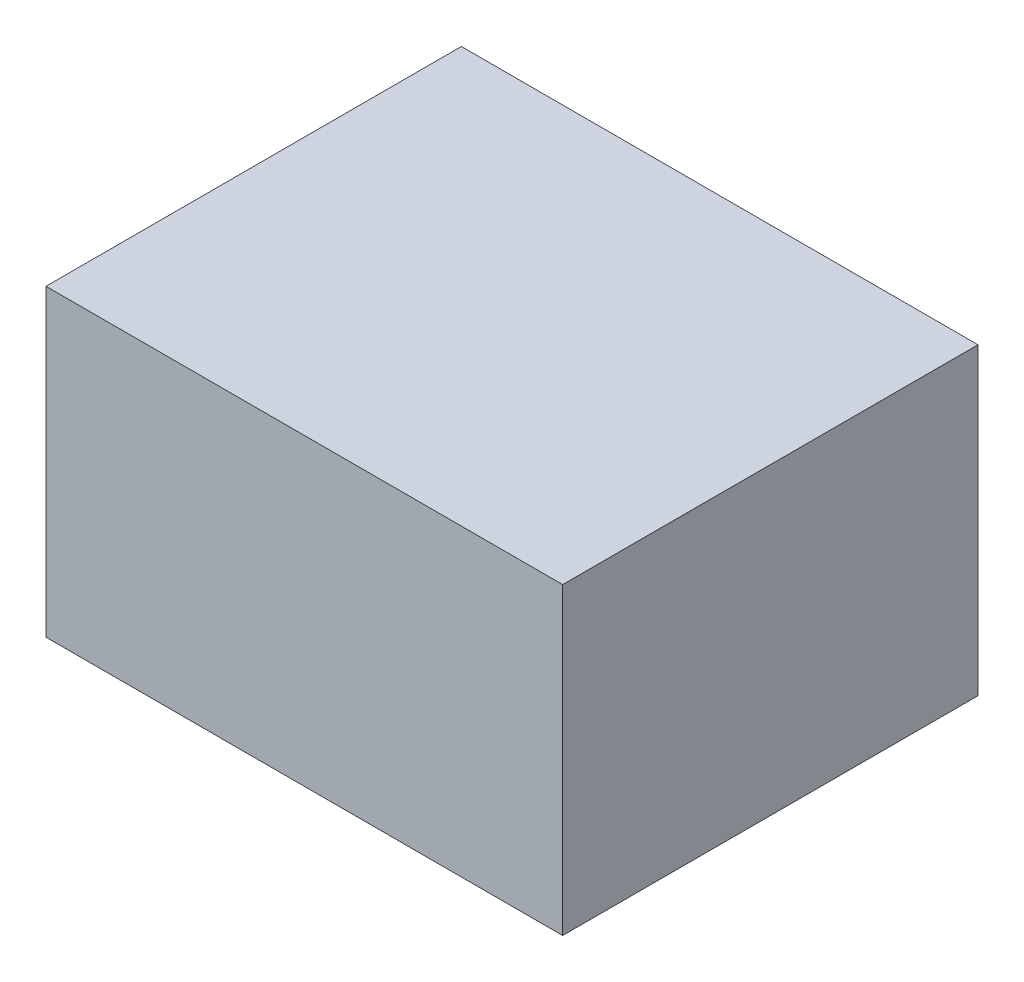
SolidWorks part; units mm, degrees
ref_plane "Front Plane" through (0, 0, 0) normal (0, 0, 1) x (1, 0, 0)
ref_plane "Top Plane" through (0, 0, 0) normal (0, 1, 0) x (1, 0, 0)
ref_plane "Right Plane" through (0, 0, 0) normal (1, 0, 0) x (0, 0, -1)
sketch "Sketch4" plane through (0, 0, 0) normal (0, 1, 0) x (1, 0, 0)
  line L1 (-102, 82) -> (102, 82)
  line L2 (-102, 82) -> (-102, -82)
  line L3 (-102, -82) -> (102, -82)
  line L4 (102, 82) -> (102, -82)
  line L5 (-102, 82) -> (102, -82) construction
  line L6 (-102, -82) -> (102, 82) construction
  point P0 (0, 0)
  dimension "D1" = 164
  dimension "D2" = 204
extrude "Boss-Extrude3" add sketch "Sketch4" along normal blind 120
sketch "Sketch5" plane through (0, 0, 0) normal (0, 1, 0) x (1, 0, 0)
  line L1 (-100, 80) -> (100, 80)
  line L2 (-100, 80) -> (-100, -80)
  line L3 (-100, -80) -> (100, -80)
  line L4 (100, 80) -> (100, -80)
  line L5 (-100, 80) -> (100, -80) construction
  line L6 (-100, -80) -> (100, 80) construction
  point P0 (0, 0)
  dimension "D1" = 160
  dimension "D2" = 200
extrude "Cut-Extrude2" cut sketch "Sketch5" along normal blind 116
